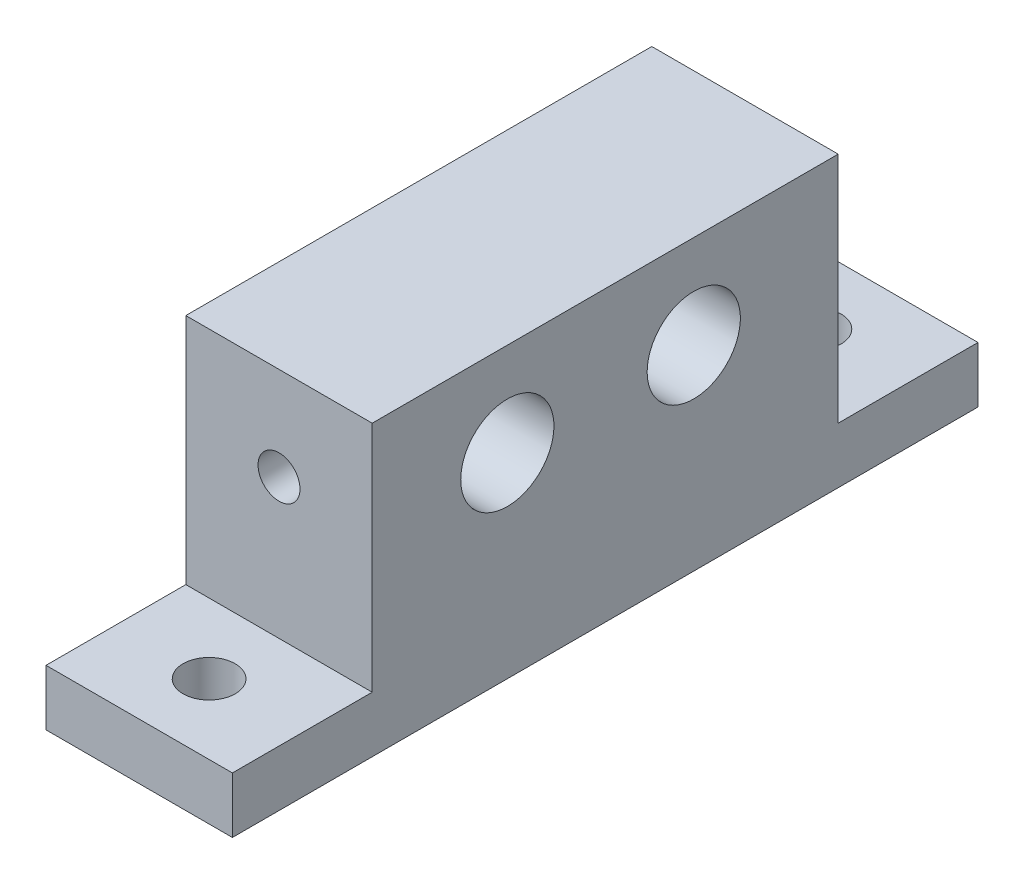
SolidWorks part; units mm, degrees
ref_plane "정면" through (0, 0, 0) normal (0, 0, 1) x (1, 0, 0)
ref_plane "윗면" through (0, 0, 0) normal (0, 1, 0) x (1, 0, 0)
ref_plane "우측면" through (0, 0, 0) normal (1, 0, 0) x (0, 0, -1)
sketch "스케치1" plane through (0, 0, 0) normal (0, 1, 0) x (1, 0, 0)
  line L1 (-9.094, 23.104) -> (0.906, 23.104)
  line L2 (-9.094, 23.104) -> (-9.094, -1.896)
  line L3 (-9.094, -1.896) -> (0.906, -1.896)
  line L4 (0.906, 23.104) -> (0.906, -1.896)
  line L5 (-9.094, 23.104) -> (0.906, -1.896) construction
  line L6 (-9.094, -1.896) -> (0.906, 23.104) construction
  point P0 (-4.094, 10.604)
  dimension "D1" = 25
  dimension "D2" = 10
extrude "보스-돌출1" add sketch "스케치1" along normal blind 10
sketch "스케치2" plane through (-9.094, 0, 0) normal (-1, 0, 0) x (0, 0, 1)
  line L0 (1.896, 10) -> (1.896, 0) construction
  line L1 (-23.104, 10) -> (1.896, 10) construction
  circle A0 centre (-5.354, 5) radius 2.5
  circle A1 centre (-15.354, 5) radius 2.5
  dimension "D1" = 5
  dimension "D2" = 5
  dimension "D5" = 5
  dimension "D6" = 5
  dimension "D3" = 10
  dimension "D4" = 7.25
extrude "컷-돌출1" cut sketch "스케치2" against normal blind 10
sketch "스케치3" plane through (0, 0, 1.896) normal (0, 0, 1) x (1, 0, 0)
  line L0 (0.906, 10) -> (0.906, 0) construction
  line L3 (-9.094, 0) -> (0.906, 0) construction
  circle A0 centre (-4.094, 5) radius 1.125
  dimension "D1" = 5
  dimension "D3" = 2.25
  dimension "D2" = 5
extrude "컷-돌출2" cut sketch "스케치3" against normal up to surface (4.75 mm away) up to face at (0.906, 5, -2.854)
sketch "스케치4" plane through (0, 0, -23.104) normal (0, 0, -1) x (-1, 0, 0)
  line L0 (-0.906, 0) -> (9.094, 0) construction
  line L1 (-0.906, 10) -> (-0.906, 0) construction
  circle A0 centre (4.094, 5) radius 1.125
  dimension "D1" = 2.25
  dimension "D2" = 5
  dimension "D3" = 5
extrude "컷-돌출3" cut sketch "스케치4" against normal up to surface (5.25 mm away)
sketch "스케치5" plane through (0, 0, 0) normal (0, -1, 0) x (1, 0, 0)
  line L0 (0.906, 1.896) -> (0.906, -23.104) construction
  line L1 (0.906, 1.896) -> (-9.094, 1.896)
  line L2 (0.906, 1.896) -> (0.906, -23.104)
  line L3 (0.906, -23.104) -> (-9.094, -23.104)
  line L4 (-9.094, 1.896) -> (-9.094, -23.104)
  line L5 (-9.094, -23.104) -> (-9.094, 1.896) construction
  line L6 (0.906, -23.104) -> (-9.094, -23.104) construction
  dimension "D1" = 25
  dimension "D2" = 0
extrude "보스-돌출2" add sketch "스케치5" along normal blind 2.5
sketch "스케치6" plane through (0, -2.5, 0) normal (0, -1, 0) x (1, 0, 0)
  line L0 (0.906, -23.104) -> (0.906, 1.896) construction
  line L1 (0.906, -30.604) -> (-9.094, -30.604)
  line L2 (0.906, -30.604) -> (0.906, 9.396)
  line L3 (0.906, 9.396) -> (-9.094, 9.396)
  line L4 (-9.094, -30.604) -> (-9.094, 9.396)
  line L5 (-9.094, 1.896) -> (-9.094, -23.104) construction
  line L6 (0.906, 1.896) -> (-9.094, 1.896) construction
  dimension "D1" = 40
  dimension "D2" = 7.5
extrude "보스-돌출3" add sketch "스케치6" along normal blind 3
sketch "스케치7" plane through (0, -2.5, 0) normal (0, 1, 0) x (1, 0, 0)
  line L0 (0.906, 30.604) -> (0.906, 23.104) construction
  line L1 (0.906, -1.896) -> (0.906, -9.396) construction
  line L4 (0.906, -9.396) -> (-9.094, -9.396) construction
  line L5 (-9.094, 30.604) -> (0.906, 30.604) construction
  circle A0 centre (-4.094, -5.646) radius 1.4
  circle A1 centre (-4.094, 26.854) radius 1.4
  dimension "D1" = 2.8
  dimension "D2" = 2.8
  dimension "D5" = 3.75
  dimension "D6" = 3.75
  dimension "D3" = 5
  dimension "D4" = 5
extrude "컷-돌출4" cut sketch "스케치7" against normal up to surface (3 mm away) up to face at (-4.094, -5.5, -10.604)
